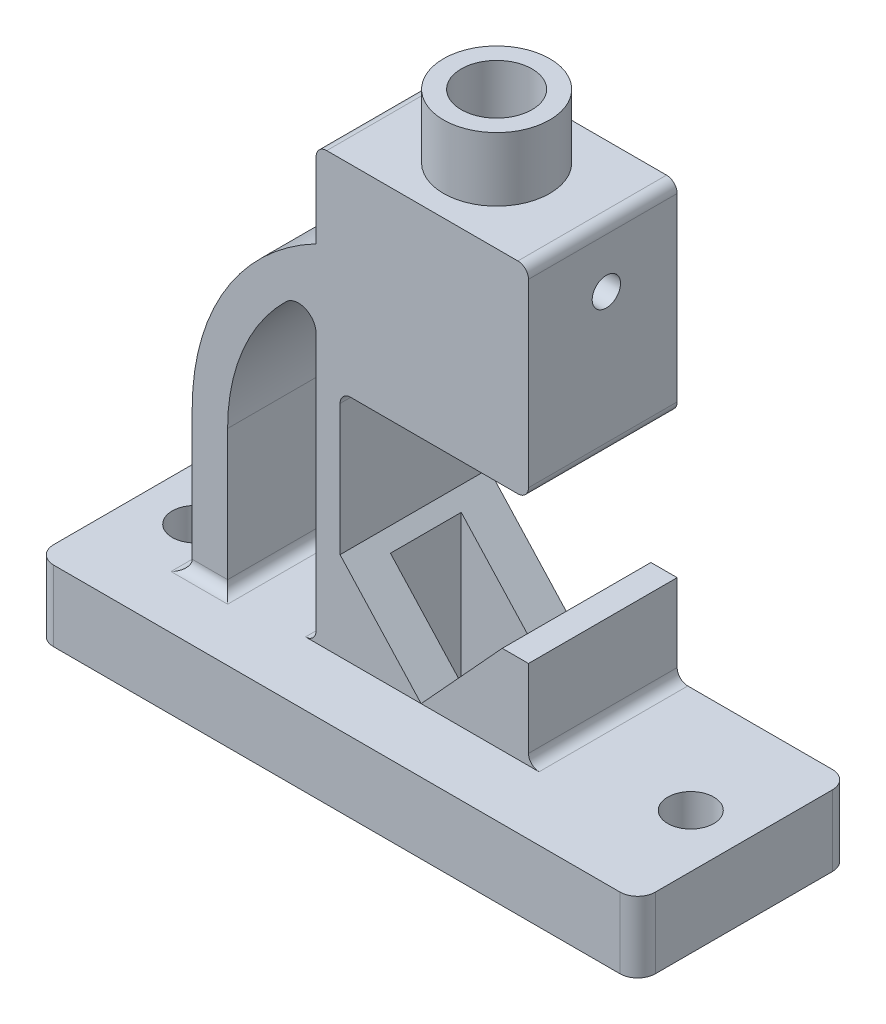
SolidWorks part; units mm, degrees
ref_plane "Front Plane" through (0, 0, 0) normal (0, 0, 1) x (1, 0, 0)
ref_plane "Top Plane" through (0, 0, 0) normal (0, 1, 0) x (1, 0, 0)
ref_plane "Right Plane" through (0, 0, 0) normal (1, 0, 0) x (0, 0, -1)
sketch "Sketch1" plane through (0, 0, 0) normal (0, 1, 0) x (1, 0, 0)
  line L1 (85, -30) -> (-85, -30)
  line L2 (85, -30) -> (85, 30)
  line L3 (85, 30) -> (-85, 30)
  line L4 (-85, -30) -> (-85, 30)
  line L5 (85, -30) -> (-85, 30) construction
  line L6 (85, 30) -> (-85, -30) construction
  point P0 (0, 0)
  dimension "D1" = 60
  dimension "D2" = 170
extrude "Boss-Extrude1" add sketch "Sketch1" along normal blind 20
fillet "Fillet1" radius 5 4 edges at (85, 10, 30) (85, 10, -30) (-85, 10, -30) (-85, 10, 30)
ref_plane "Plane1" through (0, 0, 12) normal (0, 0, -1) x (-1, 0, 0)
sketch "Sketch4" plane through (0, 0, 12) normal (0, 0, -1) x (-1, 0, 0)
  line L0 (58.8494, 20) -> (58.8494, 60)
  line L1 (80, 20) -> (-80, 20) construction
  line L2 (23.8494, 117.6628) -> (23.8494, 138.9833)
  line L3 (20.8494, 141.9833) -> (-33.1506, 141.9833)
  line L4 (-36.1506, 138.9833) -> (-36.1506, 88)
  line L5 (-33.1506, 85) -> (14.0834, 85)
  line L6 (17.0834, 82) -> (17.0834, 45)
  line L7 (17.0834, 45) -> (-5.8249, 20)
  line L8 (-5.8249, 20) -> (-28.7331, 45)
  line L9 (-28.7331, 45) -> (-36.1506, 45)
  line L10 (-36.1506, 45) -> (-36.1506, 20)
  line L11 (48.8494, 20) -> (48.8494, 60)
  line L12 (23.8494, 95.7071) -> (23.8494, 20)
  line L13 (-5.8249, 50.5949) -> (-5.8249, 20) construction
  line L14 (17.0834, 45) -> (-28.7331, 45) construction
  line L15 (80, 0) -> (-80, 0) construction
  line L16 (58.8494, 20) -> (48.8494, 20)
  line L17 (23.8494, 20) -> (-36.1506, 20)
  arc A0 (58.8494, 60) -> (23.8494, 117.6628) centre (-6.1506, 60) ccw
  arc A1 (23.8494, 138.9833) -> (20.8494, 141.9833) centre (20.8494, 138.9833) ccw
  arc A2 (-33.1506, 141.9833) -> (-36.1506, 138.9833) centre (-33.1506, 138.9833) ccw
  arc A3 (-36.1506, 88) -> (-33.1506, 85) centre (-33.1506, 88) ccw
  arc A4 (14.0834, 85) -> (17.0834, 82) centre (14.0834, 82) cw
  arc A5 (48.8494, 60) -> (32.3494, 99.2779) centre (-6.1506, 60) ccw
  arc A6 (32.3494, 99.2779) -> (23.8494, 95.7071) centre (28.8494, 95.7071) ccw
  dimension "D6" = 3
  dimension "D7" = 60
  dimension "D8" = 65
  dimension "D9" = 55
  dimension "D10" = 5
  dimension "D1" = 25
  dimension "D2" = 40
  dimension "D3" = 25
  dimension "D4" = 60
  dimension "D5" = 85
  dimension "D11" = 56.9833
  dimension "D12" = 17.0834
  dimension "D13" = 23.8494
extrude "Boss-Extrude2" add sketch "Sketch4" along normal up to surface (42 mm away) contours A6 A5 L11 L16 L0 A0 L2 A1 L3 A2 L4 A3 L5 A4 L6 L7 L17 L12 | L17 L8 L9 L10 up to face at (0, 10, -30)
sketch "Sketch5" plane through (0, 141.9833, 0) normal (0, 1, 0) x (1, 0, 0)
  line L0 (-20.8494, 30) -> (-20.8494, -12) construction
  line L3 (33.1506, 30) -> (-20.8494, 30) construction
  circle A0 centre (6.1506, 9) radius 15
  dimension "D3" = 30
  dimension "D1" = 27
  dimension "D2" = 21
extrude "Boss-Extrude3" add sketch "Sketch5" along normal blind 18
sketch "Sketch6" plane through (0, 159.9833, 0) normal (0, 1, 0) x (1, 0, 0)
  circle A0 centre (6.1506, 9) radius 10
  dimension "D1" = 20
extrude "Cut-Extrude1" cut sketch "Sketch6" against normal blind 28
ref_plane "Plane2" through (0, 0, -9) normal (0, 0, -1) x (-1, 0, 0)
sketch "Sketch7" plane through (0, 0, -9) normal (0, 0, -1) x (-1, 0, 0)
  line L0 (-80, 0) -> (80, 0) construction
  line L1 (-26.1506, 0) -> (13.8494, 0)
  line L2 (-26.1506, 0) -> (-26.1506, 131.9833)
  line L3 (-26.1506, 131.9833) -> (13.8494, 131.9833)
  line L4 (13.8494, 0) -> (13.8494, 131.9833)
  line L5 (-6.1506, 159.9833) -> (-6.1506, 141.9833) construction
  line L6 (-6.1506, 166.8178) -> (-6.1506, -16.1316) construction
  line L7 (-6.1506, 131.9833) -> (-6.1506, 159.9833) construction
  line L8 (-33.1506, 141.9833) -> (20.8494, 141.9833) construction
  dimension "D1" = 40
  dimension "D2" = 10
extrude "Cut-Extrude2" cut sketch "Sketch7" against normal mid plane 20
fillet "Fillet5" radius 3 5 edges at (36.1506, 20, -9) (-23.8494, 20, -9) (-48.8494, 20, -9) (-53.8494, 20, 12) (-58.8494, 20, -9)
sketch "Sketch8" plane through (0, 20, 0) normal (0, 1, 0) x (1, 0, 0)
  line L3 (0, 61.6945) -> (0, -81.2434) construction
  circle A0 centre (-70, 0) radius 6.5
  circle A1 centre (70, 0) radius 6.5
  dimension "D1" = 13
  dimension "D2" = 140
extrude "Cut-Extrude3" cut sketch "Sketch8" against normal up to surface (20 mm away) up to face at (6.1506, 0, -9)
sketch "Sketch9" plane through (36.1506, 0, 0) normal (1, 0, 0) x (0, 0, -1)
  line L0 (30, 88) -> (30, 138.9833) construction
  line L1 (19, 159.9833) -> (-1, 159.9833) construction
  circle A0 centre (10, 124.9833) radius 4
  dimension "D1" = 8
  dimension "D2" = 20
  dimension "D3" = 35
extrude "Cut-Extrude4" cut sketch "Sketch9" against normal up to surface (60 mm away) up to face at (-23.8494, 128.3231, -9)
